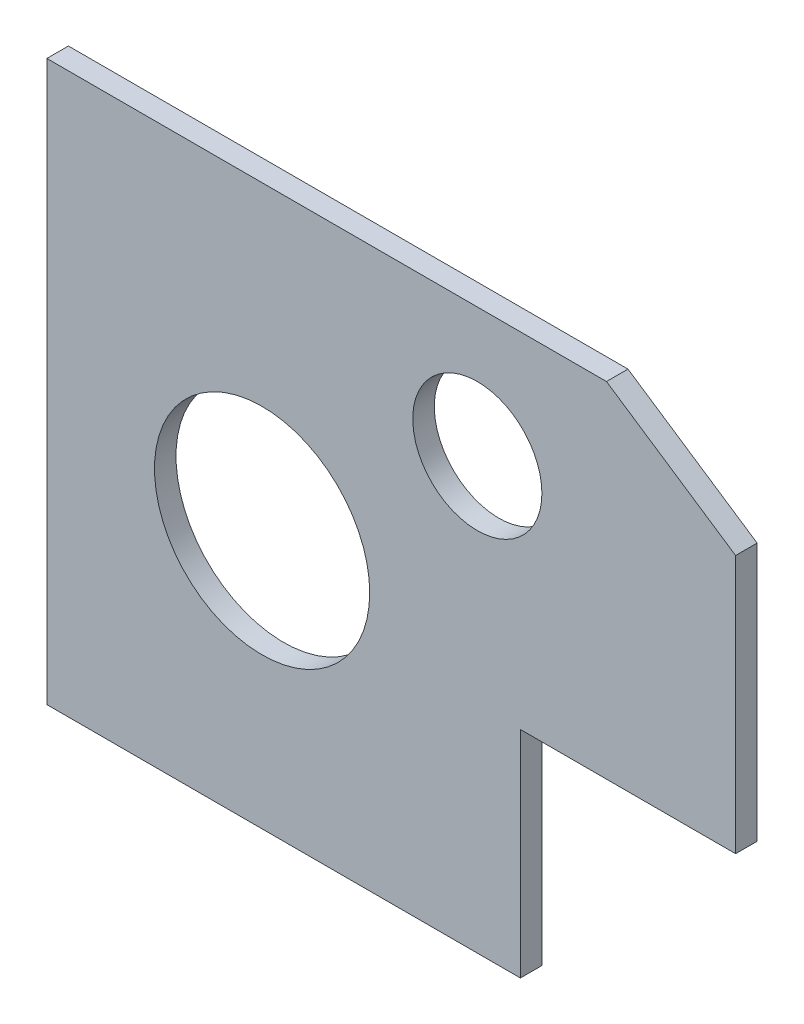
SolidWorks part; units mm, degrees
ref_plane "Front Plane" through (0, 0, 0) normal (0, 0, 1) x (1, 0, 0)
ref_plane "Top Plane" through (0, 0, 0) normal (0, 1, 0) x (1, 0, 0)
ref_plane "Right Plane" through (0, 0, 0) normal (1, 0, 0) x (0, 0, -1)
sketch "Model" plane through (0, 0, 0) normal (0, 0, 1) x (1, 0, 0)
  line L0 (0, 0) -> (0, 165.1)
  line L1 (0, 165.1) -> (165.1, 165.1)
  line L2 (0, 0) -> (139.7, 0)
  line L3 (139.7, 0) -> (139.7, 63.5)
  line L4 (139.7, 63.5) -> (203.2, 63.5)
  line L5 (203.2, 63.5) -> (203.2, 139.7)
  line L6 (203.2, 139.7) -> (165.1, 165.1)
  circle A0 centre (63.5, 76.2) radius 31.75
  circle A1 centre (127, 127) radius 19.05
sketch "Sketch2" plane through (0, 0, 0) normal (0, 0, 1) x (1, 0, 0)
  line L0 (0, 0) -> (0, 165.1)
  line L1 (0, 165.1) -> (165.1, 165.1)
  line L2 (0, 0) -> (139.7, 0)
  line L3 (139.7, 0) -> (139.7, 63.5)
  line L4 (139.7, 63.5) -> (203.2, 63.5)
  line L5 (203.2, 63.5) -> (203.2, 139.7)
  line L6 (203.2, 139.7) -> (165.1, 165.1)
  circle A0 centre (63.5, 76.2) radius 31.75
  circle A1 centre (127, 127) radius 19.05
  dimension "D6" = 38.1
  dimension "D7" = 63.5
  dimension "D1" = 165.1
  dimension "D2" = 165.1
  dimension "D3" = 76.2
  dimension "D4" = 63.5
  dimension "D5" = 139.7
extrude "Boss-Extrude1" add sketch "Sketch2" along normal blind 6.35
